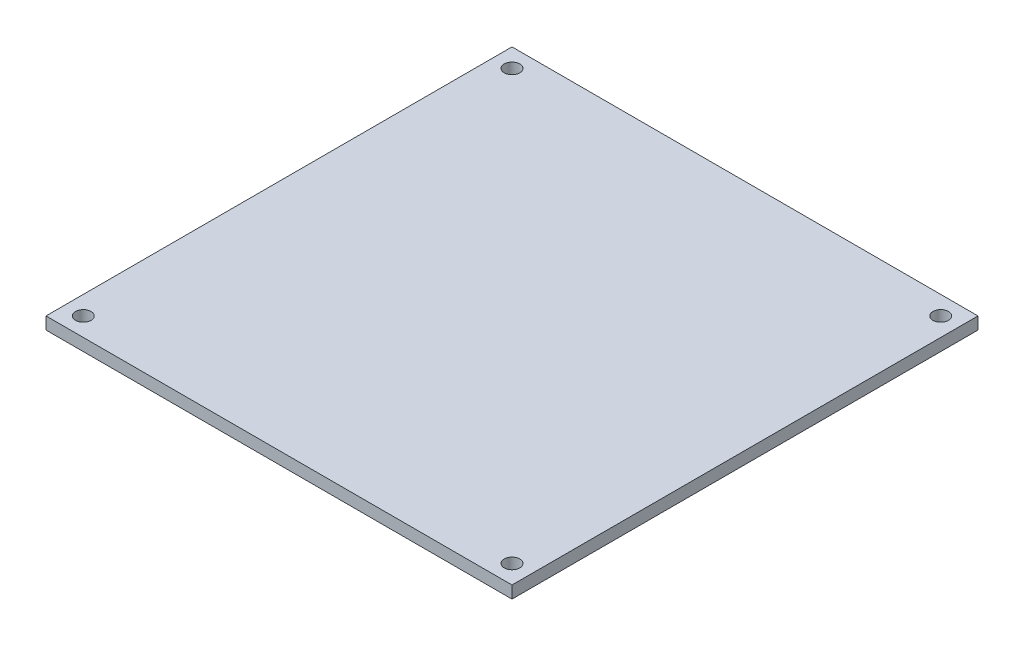
SolidWorks part; units mm, degrees
ref_plane "Front Plane" through (0, 0, 0) normal (0, 0, 1) x (1, 0, 0)
ref_plane "Top Plane" through (0, 0, 0) normal (0, 1, 0) x (1, 0, 0)
ref_plane "Right Plane" through (0, 0, 0) normal (1, 0, 0) x (0, 0, -1)
sketch "Sketch1" plane through (0, 0, 0) normal (0, 1, 0) x (1, 0, 0)
  line L1 (38.1, -38.1) -> (-38.1, -38.1)
  line L2 (38.1, -38.1) -> (38.1, 38.1)
  line L3 (38.1, 38.1) -> (-38.1, 38.1)
  line L4 (-38.1, -38.1) -> (-38.1, 38.1)
  line L5 (38.1, -38.1) -> (-38.1, 38.1) construction
  line L6 (38.1, 38.1) -> (-38.1, -38.1) construction
  circle A0 centre (-35.052, 35.052) radius 1.27
  circle A1 centre (35.052, 35.052) radius 1.27
  circle A2 centre (-35.052, -35.052) radius 1.27
  circle A3 centre (35.052, -35.052) radius 1.27
  point P0 (0, 0)
  dimension "D3" = 3.048
  dimension "D7" = 2.54
  dimension "D8" = 2.54
  dimension "D9" = 2.54
  dimension "D10" = 2.54
  dimension "D1" = 76.2
  dimension "D2" = 76.2
  dimension "D4" = 3.048
  dimension "D5" = 3.048
  dimension "D6" = 3.048
extrude "Boss-Extrude1" add sketch "Sketch1" along normal blind 2.0066
